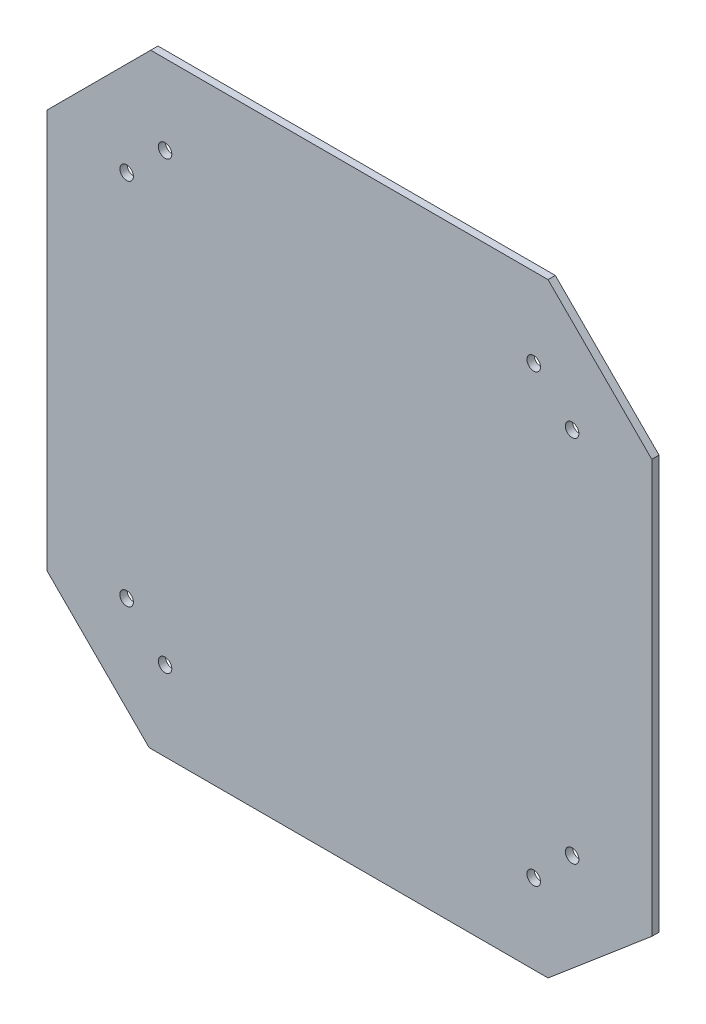
SolidWorks part; units mm, degrees
material "C-Glass Fiber"
ref_plane "Front Plane" through (0, 0, 0) normal (0, 0, 1) x (1, 0, 0)
ref_plane "Top Plane" through (0, 0, 0) normal (0, 1, 0) x (1, 0, 0)
ref_plane "Right Plane" through (0, 0, 0) normal (1, 0, 0) x (0, 0, -1)
sketch "Sketch1" plane through (0, 0, 0) normal (0, 0, 1) x (1, 0, 0)
  line L0 (0, -70.857) -> (0, 87.2635) construction
  line L1 (-94.5157, 0) -> (123.9998, 0) construction
  line L2 (62.5, 93.2079) -> (62.5, -95.5857) construction
  line L3 (-62.5, 98.439) -> (-62.5, -97.9634) construction
  line L4 (164.1839, -62.5) -> (-145.6374, -62.5) construction
  line L5 (158.0017, 62.5) -> (-146.593, 62.5) construction
  line L6 (-62.5, 62.5) -> (62.5, 62.5)
  line L7 (62.5, 62.5) -> (62.5, -62.5)
  line L8 (-62.5, 62.5) -> (-62.5, -62.5)
  line L9 (-62.5, -62.5) -> (62.5, -62.5)
  line L10 (46.0375, -92.075) -> (46.0375, 65.0875) construction
  line L11 (38.1, -103.1875) -> (38.1, 68.2625) construction
  line L12 (109.5375, -46.0375) -> (-92.0129, -46.0375) construction
  line L13 (111.125, -38.1) -> (-89.1956, -38.1) construction
  line L14 (-46.0375, -103.1875) -> (-46.0375, 68.2625) construction
  line L15 (-38.1, -98.425) -> (-38.1, 73.025) construction
  line L16 (101.6, 46.0375) -> (-93.6625, 46.0375) construction
  line L17 (101.6, 38.1) -> (-95.25, 38.1) construction
  circle A0 centre (46.0375, 38.1) radius 1.4
  circle A1 centre (38.1, 46.0375) radius 1.4
  circle A2 centre (-38.1, 46.0375) radius 1.4
  circle A3 centre (-46.0375, 38.1) radius 1.4
  circle A4 centre (-46.0375, -38.1) radius 1.4
  circle A5 centre (-38.1, -46.0375) radius 1.4
  circle A6 centre (38.1, -46.0375) radius 1.4
  circle A7 centre (46.0375, -38.1) radius 1.4
  dimension "D1" = 62.5
  dimension "D2" = 125
  dimension "D3" = 62.5
  dimension "D4" = 125
  dimension "D5" = 38.1
  dimension "D6" = 46.0375
  dimension "D7" = 46.0375
  dimension "D8" = 38.1
  dimension "D9" = 46.0375
  dimension "D10" = 38.1
  dimension "D11" = 38.1
  dimension "D12" = 46.0375
extrude "Extrude1" add sketch "Sketch1" along normal blind 1.5
sketch "Sketch2" plane through (0, 0, 1.5) normal (0, 0, 1) x (1, 0, 0)
  line L0 (41.0631, -62.5) -> (62.5, -44.3386)
  line L1 (62.5, -62.5) -> (62.5, 62.5) construction
  line L3 (-62.5, -62.5) -> (62.5, -62.5) construction
  line L4 (62.5, -44.3386) -> (62.5, -62.5)
  line L5 (41.0631, 62.5) -> (62.5, 41.0631)
  line L6 (62.5, 62.5) -> (-62.5, 62.5) construction
  line L7 (62.5, 41.0631) -> (62.5, 62.5)
  line L8 (62.5, 62.5) -> (41.0631, 62.5)
  line L9 (62.5, -62.5) -> (41.0631, -62.5)
  line L10 (-41.3842, -62.5) -> (-62.5, -41.3842)
  line L11 (-62.5, 62.5) -> (-62.5, -62.5) construction
  line L12 (-62.5, -41.3842) -> (-62.5, -62.5)
  line L13 (-62.5, -62.5) -> (-41.3842, -62.5)
  line L14 (-62.5, 41.0631) -> (-41.0631, 62.5)
  line L15 (-41.0631, 62.5) -> (-62.5, 62.5)
  line L16 (-62.5, 62.5) -> (-62.5, 41.0631)
extrude "Extrude2" cut sketch "Sketch2" against normal blind 10
